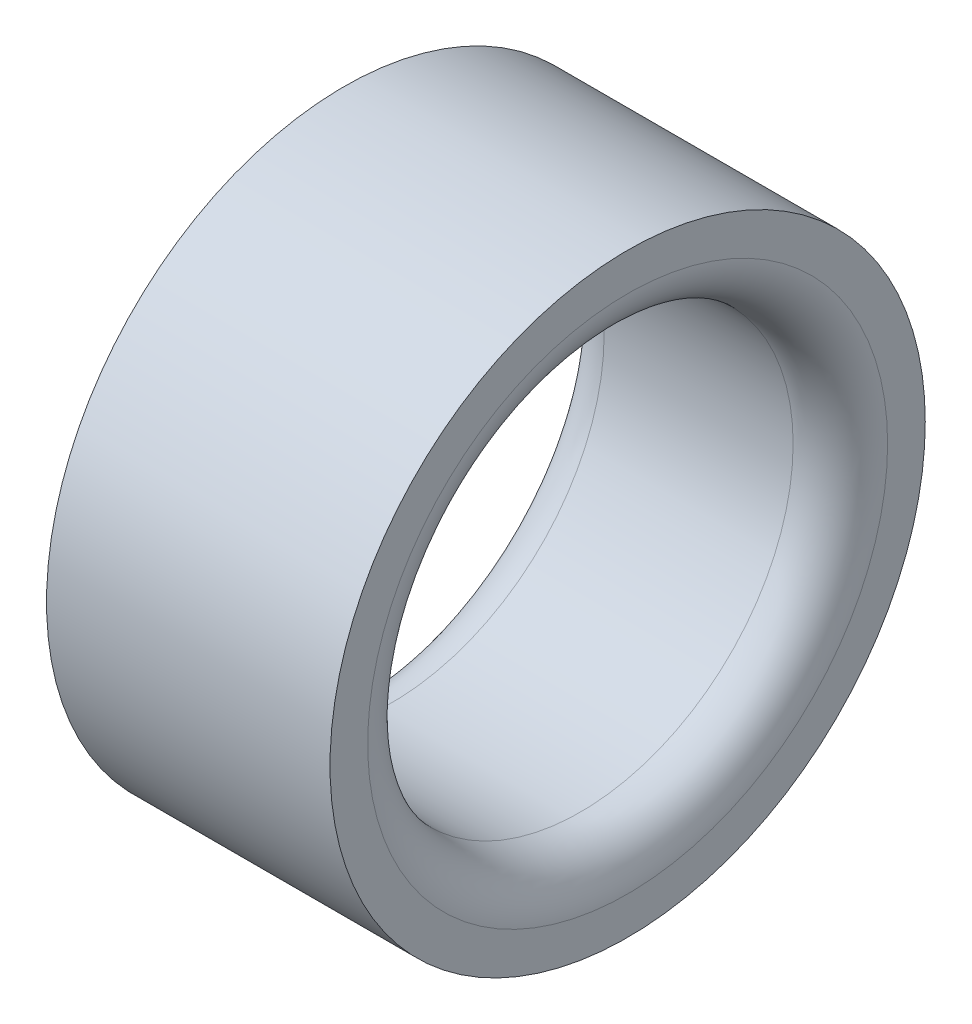
SolidWorks part; units mm, degrees
material "6061-T6 (SS)"
ref_plane "Front Plane" through (0, 0, 0) normal (0, 0, 1) x (1, 0, 0)
ref_plane "Top Plane" through (0, 0, 0) normal (0, 1, 0) x (1, 0, 0)
ref_plane "Right Plane" through (0, 0, 0) normal (1, 0, 0) x (0, 0, -1)
sketch "Sketch1" plane through (0, 0, 0) normal (1, 0, 0) x (0, 0, -1)
  circle A0 centre (0, 0) radius 20
  circle A1 centre (0, 0) radius 14.2949
  dimension "D1" = 40
  dimension "D2" = 28.5898
extrude "Boss-Extrude1" add sketch "Sketch1" along normal blind 19.05
fillet "Fillet1" radius 3.175 2 edges at (0, 0, -14.2949) (19.05, 0, -14.2949)
equation "\"Thick\"= \"in\""
